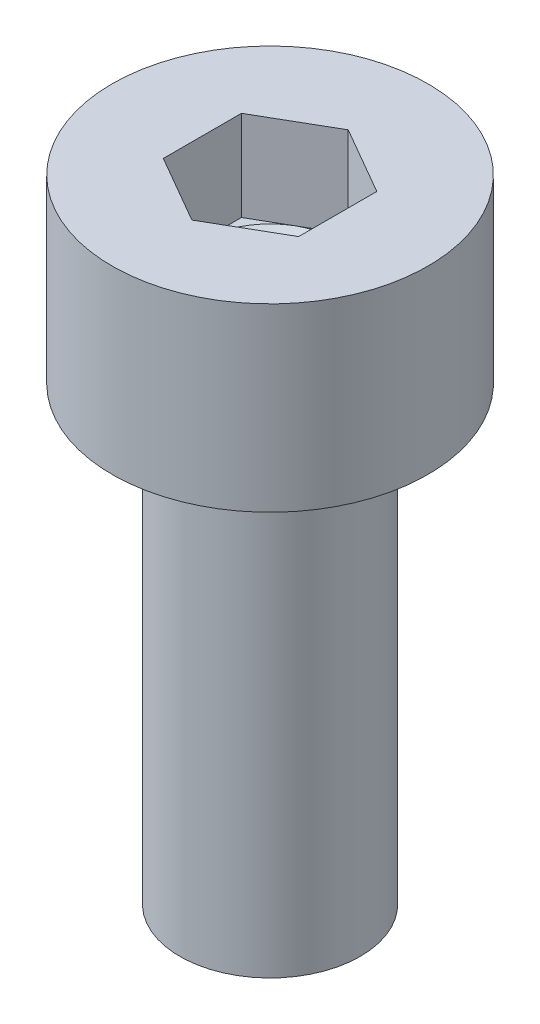
SolidWorks part; units mm, degrees
ref_plane "Front Plane" through (0, 0, 0) normal (0, 0, 1) x (1, 0, 0)
ref_plane "Top Plane" through (0, 0, 0) normal (0, 1, 0) x (1, 0, 0)
ref_plane "Right Plane" through (0, 0, 0) normal (1, 0, 0) x (0, 0, -1)
sketch "Sketch1" plane through (0, 0, 0) normal (0, 0, 1) x (1, 0, 0)
  line L0 (0, 0) -> (3.5, 0)
  line L1 (3.5, 0) -> (3.5, -4)
  line L2 (3.5, -4) -> (2, -4)
  line L3 (2, -4) -> (2, -14)
  line L4 (2, -14) -> (0, -14)
  line L5 (0, -14) -> (0, 0)
  line L7 (0, 0) -> (0, -14) construction
  dimension "CS_A" = 7
  dimension "CS_L" = 10
  dimension "CS_M" = 4
  dimension "CS_E" = 4
revolve "Revolve1" add sketch "Sketch1" angle 360 about L7
cosmetic thread "Cosmetic Thread1" parameters "CS_D_s"=3.242
sketch "Sketch2" plane through (0, 0, 0) normal (0, 0, 1) x (1, 0, 0)
  line L0 (1.5, 0) -> (1.5, -2)
  line L1 (1.5, -2) -> (0, -2.866)
  line L2 (0, -2.866) -> (0, 0)
  line L3 (0, 0) -> (1.5, 0)
  line L4 (0, 0) -> (0, -2.866) construction
  dimension "D1" = 60
  dimension "CS_B" = 3
  dimension "CS_T_s" = 2
revolve "Cut-Revolve1" cut sketch "Sketch2" angle 360 about L4
sketch "Sketch3" plane through (0, 0, 0) normal (0, 1, 0) x (1, 0, 0)
  line L1 (0, 1.7321) -> (-1.5, 0.866)
  line L2 (-1.5, 0.866) -> (-1.5, -0.866)
  line L3 (-1.5, -0.866) -> (0, -1.7321)
  line L4 (0, -1.7321) -> (1.5, -0.866)
  line L5 (1.5, -0.866) -> (1.5, 0.866)
  line L6 (1.5, 0.866) -> (0, 1.7321)
  circle A0 centre (0, 0) radius 1.5 construction
extrude "Cut-Extrude1" cut sketch "Sketch3" against normal blind 2
